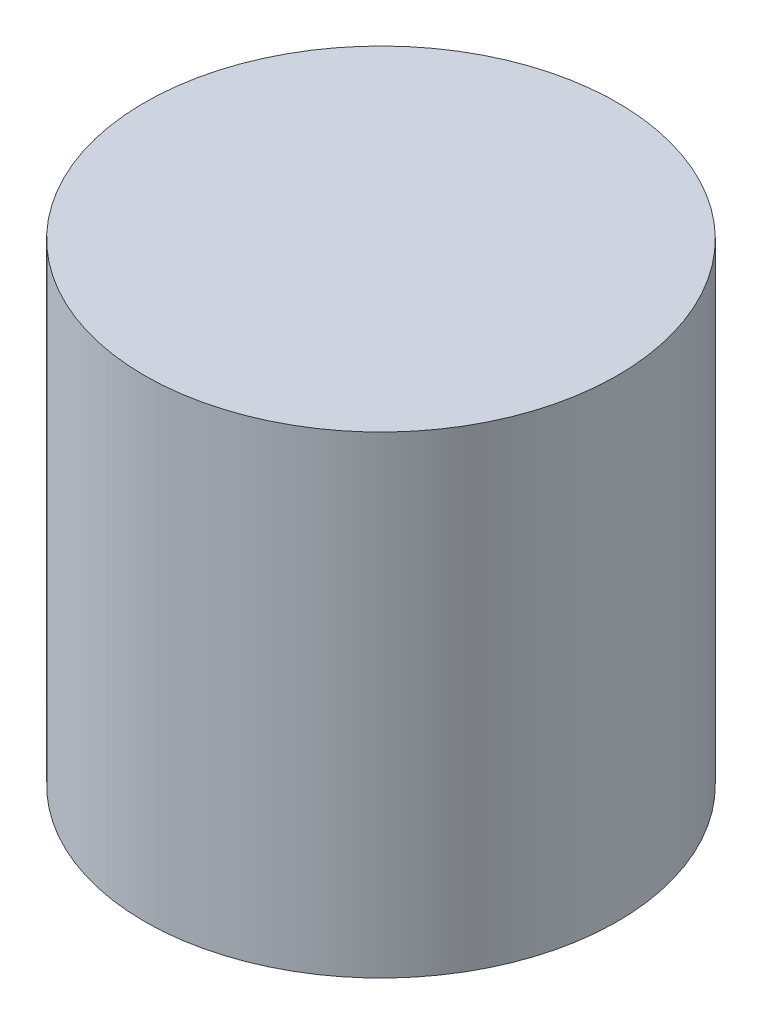
SolidWorks part; units mm, degrees
ref_plane "Front Plane" through (0, 0, 0) normal (0, 0, 1) x (1, 0, 0)
ref_plane "Top Plane" through (0, 0, 0) normal (0, 1, 0) x (1, 0, 0)
ref_plane "Right Plane" through (0, 0, 0) normal (1, 0, 0) x (0, 0, -1)
sketch "Sketch1" plane through (0, 0, 0) normal (0, 1, 0) x (1, 0, 0)
  circle A0 centre (0, 0) radius 25.4
  dimension "D1" = 50.8
extrude "Boss-Extrude1" add sketch "Sketch1" along normal blind 50.8
